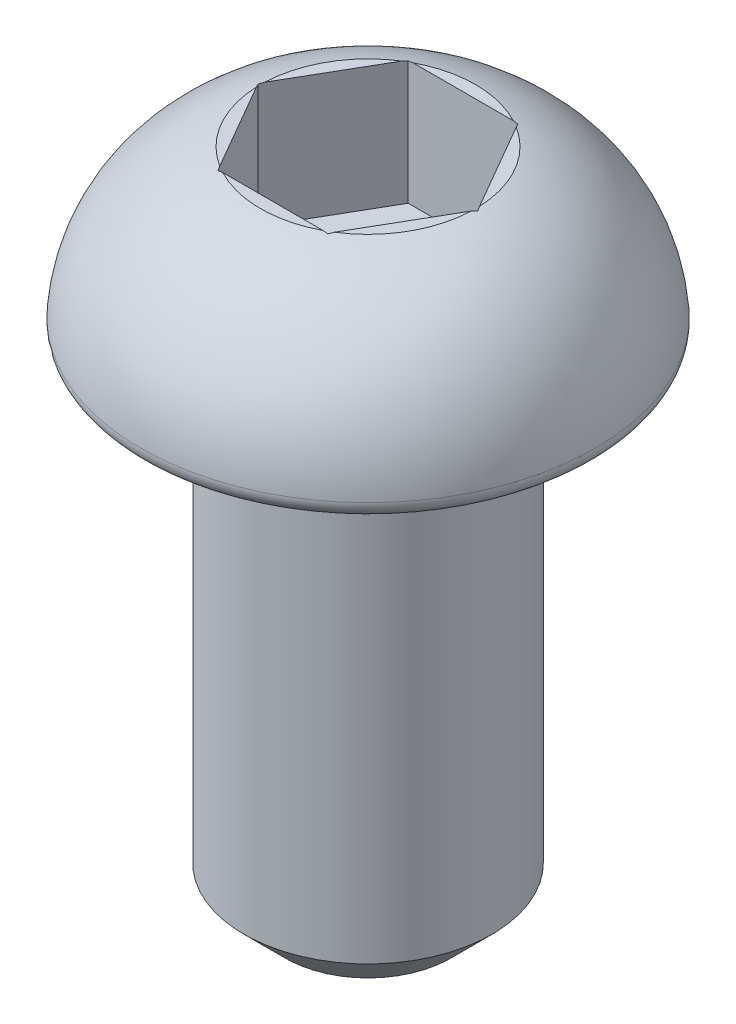
SolidWorks part; units mm, degrees
ref_plane "前视" through (0, 0, 0) normal (0, 0, 1) x (1, 0, 0)
ref_plane "上视" through (0, 0, 0) normal (0, 1, 0) x (1, 0, 0)
ref_plane "右视" through (0, 0, 0) normal (1, 0, 0) x (0, 0, -1)
sketch "草图1" plane through (0, 0, 0) normal (0, 0, 1) x (1, 0, 0)
  line L0 (0, 0) -> (0, 2)
  line L1 (0, 2) -> (1.3, 2)
  line L2 (0, 0) -> (2.75, 0)
  arc A0 (1.3, 2) -> (2.75, 0) centre (0.7515, 0.0767) cw
  dimension "D4" = 2
  dimension "D1" = 1.3
  dimension "D2" = 2.75
  dimension "D3" = 2
revolve "旋转1" add sketch "草图1" angle 360 about L0
fillet "圆角1" radius 0.2 1 edges at (0, 0, -2.75)
sketch "草图2" plane through (0, 2, 0) normal (0, 1, 0) x (1, 0, 0)
  line L1 (1.3279, 0) -> (0.664, 1.15)
  line L2 (0.664, 1.15) -> (-0.664, 1.15)
  line L3 (-0.664, 1.15) -> (-1.3279, 0)
  line L4 (-1.3279, 0) -> (-0.664, -1.15)
  line L5 (-0.664, -1.15) -> (0.664, -1.15)
  line L6 (0.664, -1.15) -> (1.3279, 0)
  circle A0 centre (0, 0) radius 1.15 construction
  dimension "D1" = 2.3
extrude "切除-拉伸1" cut sketch "草图2" against normal blind 1.5
sketch "草图3" plane through (0, 0, 0) normal (0, -1, 0) x (1, 0, 0)
  circle A0 centre (0, 0) radius 1.5
  dimension "D1" = 3
extrude "凸台-拉伸1" add sketch "草图3" along normal blind 6
chamfer "倒角1" distance 0.5 angle 45 1 edges at (0, -6, -1.5)
